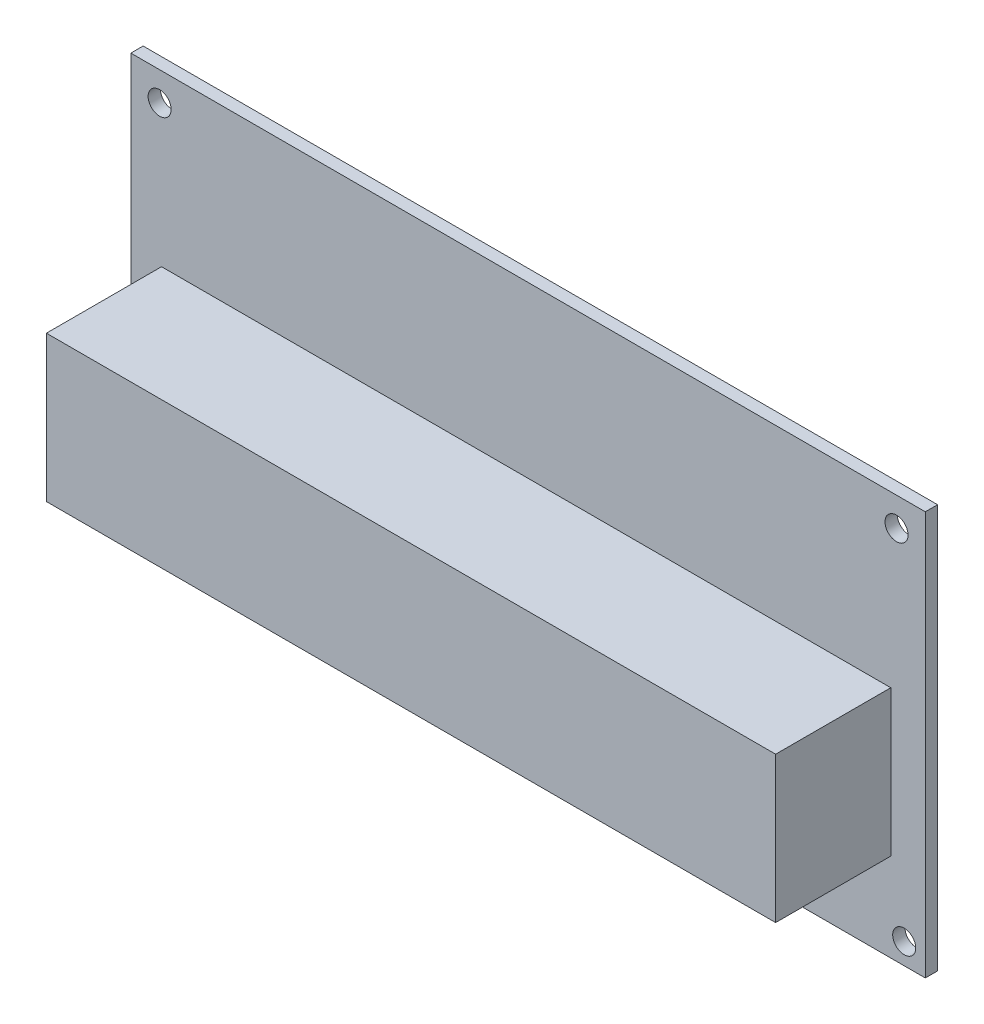
SolidWorks part; units mm, degrees
ref_plane "Plan de face" through (0, 0, 0) normal (0, 0, 1) x (1, 0, 0)
ref_plane "Plan de dessus" through (0, 0, 0) normal (0, 1, 0) x (1, 0, 0)
ref_plane "Plan de droite" through (0, 0, 0) normal (1, 0, 0) x (0, 0, -1)
sketch "Esquisse2" plane through (0, 0, 0) normal (0, 0, 1) x (1, 0, 0)
  line L0 (-51.75, -26.3) -> (51.75, -26.3)
  line L3 (-51.75, 26.3) -> (51.75, 26.3)
  line L4 (51.75, -26.3) -> (51.75, 26.3)
  line L5 (-51.75, -26.3) -> (-51.75, 26.3)
  circle A0 centre (48, 22.55) radius 1.5
  circle A1 centre (49, -23.55) radius 1.5
  circle A2 centre (-49, -23.55) radius 1.5
  circle A3 centre (-48, 22.55) radius 1.5
  point P18 (0, 0)
  dimension "D3" = 3
  dimension "D10" = 3
  dimension "D11" = 3
  dimension "D12" = 3
  dimension "D1" = 103.5
  dimension "D2" = 52.6
  dimension "D4" = 3.75
  dimension "D5" = 3.75
  dimension "D6" = 96
  dimension "D7" = 51.75
  dimension "D8" = 26.3
  dimension "D9" = 3.75
  dimension "D13" = 2.75
  dimension "D14" = 2.75
  dimension "D15" = 2.75
  dimension "D16" = 2.75
extrude "Boss.-Extru.1" add sketch "Esquisse2" along normal blind 1.6
sketch "Esquisse3" plane through (0, 0, 1.6) normal (0, 0, 1) x (1, 0, 0)
  line L0 (-51.75, 26.3) -> (-51.75, -26.3) construction
  line L1 (-47.75, -14.8) -> (47.25, -14.8)
  line L2 (-47.75, -14.8) -> (-47.75, 4.2)
  line L3 (-47.75, 4.2) -> (47.25, 4.2)
  line L4 (47.25, -14.8) -> (47.25, 4.2)
  line L5 (-51.75, -26.3) -> (51.75, -26.3) construction
  point P4 (41.3427, -7.4417)
  dimension "D1" = 95
  dimension "D2" = 19
  dimension "D3" = 4
  dimension "D4" = 11.5
extrude "Boss.-Extru.2" add sketch "Esquisse3" along normal blind 15
